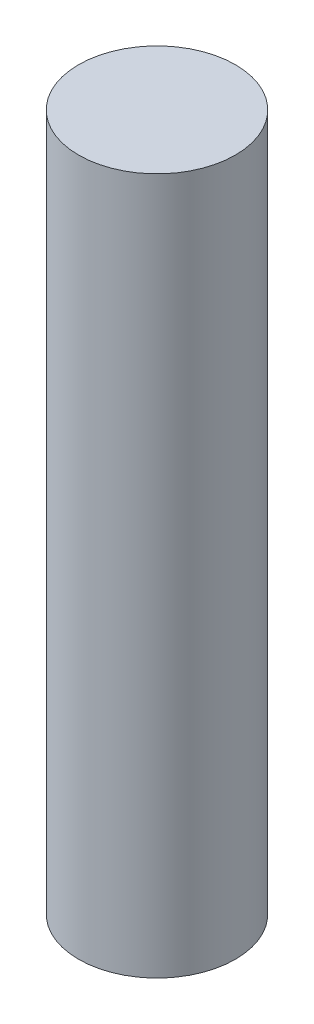
SolidWorks part; units mm, degrees
ref_plane "前视基准面" through (0, 0, 0) normal (0, 0, 1) x (1, 0, 0)
ref_plane "上视基准面" through (0, 0, 0) normal (0, 1, 0) x (1, 0, 0)
ref_plane "右视基准面" through (0, 0, 0) normal (1, 0, 0) x (0, 0, -1)
other "Configuration Table"
sketch "草图1" plane through (0, 0, 0) normal (0, 1, 0) x (1, 0, 0)
  circle A0 centre (0, 0) radius 2.25
  dimension "D1" = 4.5
extrude "凸台-拉伸1" add sketch "草图1" along normal blind 20
